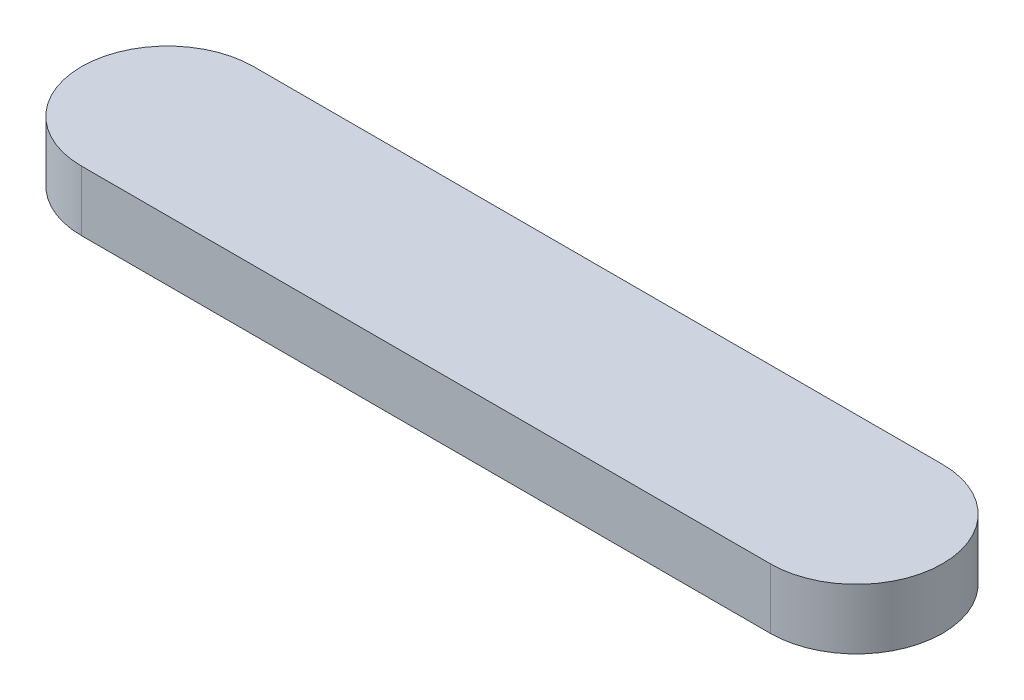
SolidWorks part; units mm, degrees
ref_plane "Front Plane" through (0, 0, 0) normal (0, 0, 1) x (1, 0, 0)
ref_plane "Top Plane" through (0, 0, 0) normal (0, 1, 0) x (1, 0, 0)
ref_plane "Right Plane" through (0, 0, 0) normal (1, 0, 0) x (0, 0, -1)
sketch "Sketch2" plane through (0, 0, 0) normal (0, 1, 0) x (1, 0, 0)
  line L0 (0, 0) -> (800, 0) construction
  line L1 (0, 100) -> (800, 100)
  line L2 (0, -100) -> (800, -100)
  arc A0 (0, 100) -> (0, -100) centre (0, 0) ccw
  arc A1 (800, -100) -> (800, 100) centre (800, 0) ccw
  point P3 (400, 0)
extrude "Boss-Extrude1" add sketch "Sketch2" along normal blind 70
sketch "Sketch3" plane through (0, 0, 0) normal (0, -1, 0) x (1, 0, 0)
  circle A0 centre (0, 0) radius 10
  point P3 (0, 0)
extrude "Boss-Extrude2" add sketch "Sketch3" along normal blind 20
sketch "Sketch4" plane through (0, 0, 0) normal (0, -1, 0) x (1, 0, 0)
  circle A1 centre (800, 0) radius 10
extrude "Boss-Extrude3" add sketch "Sketch4" along normal blind 20
